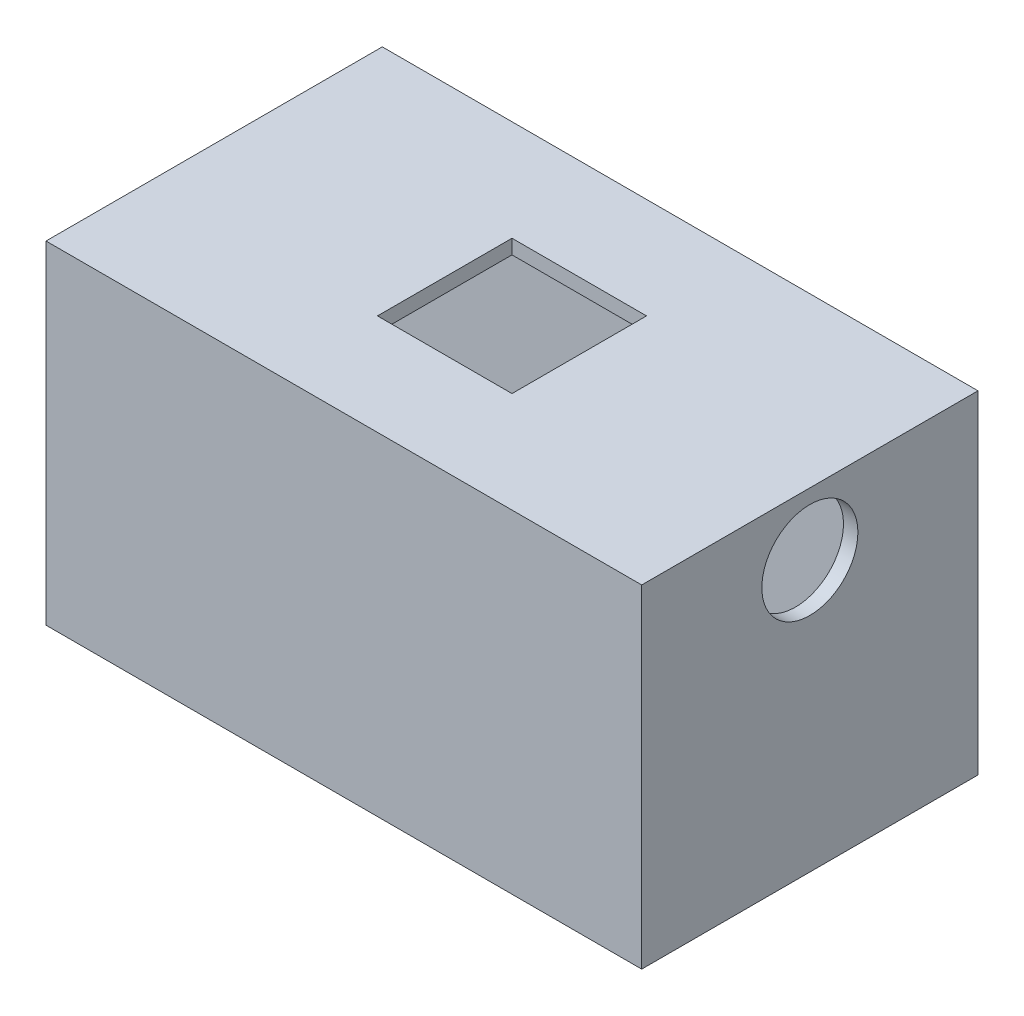
SolidWorks part; units mm, degrees
material "ABS PC"
ref_plane "前视基准面" through (0, 0, 0) normal (0, 0, 1) x (1, 0, 0)
ref_plane "上视基准面" through (0, 0, 0) normal (0, 1, 0) x (1, 0, 0)
ref_plane "右视基准面" through (0, 0, 0) normal (1, 0, 0) x (0, 0, -1)
sketch "草图1" plane through (0, 0, 0) normal (0, 1, 0) x (1, 0, 0)
  line L1 (-28.0032, 22.2518) -> (33.9968, 22.2518)
  line L2 (-28.0032, 22.2518) -> (-28.0032, -12.7482)
  line L3 (-28.0032, -12.7482) -> (33.9968, -12.7482)
  line L4 (33.9968, 22.2518) -> (33.9968, -12.7482)
  point P4 (0, 0)
  dimension "D1" = 35
  dimension "D2" = 62
extrude "凸台-拉伸1" add sketch "草图1" along normal blind 1.5
sketch "草图2" plane through (0, 0, 0) normal (0, -1, 0) x (1, 0, 0)
  line L0 (-28.0032, 12.7482) -> (33.9968, 12.7482) construction
  line L1 (-28.0032, 12.7482) -> (33.9968, 12.7482)
  line L2 (-28.0032, -22.2518) -> (-28.0032, 12.7482) construction
  line L3 (-28.0032, -22.2518) -> (-28.0032, 12.7482)
  line L4 (33.9968, -22.2518) -> (-28.0032, -22.2518) construction
  line L5 (33.9968, -22.2518) -> (-28.0032, -22.2518)
  line L6 (33.9968, 12.7482) -> (33.9968, -22.2518) construction
  line L7 (33.9968, 12.7482) -> (33.9968, -22.2518)
extrude "凸台-拉伸2" add sketch "草图2" along normal up to surface (30.6292 mm away)
sketch "草图3" plane through (0, -30.6292, 0) normal (0, -1, 0) x (1, 0, 0)
  line L0 (32.4968, -20.7518) -> (32.4968, 11.2482) construction
  line L1 (-26.5032, -20.7518) -> (32.4968, -20.7518) construction
  line L2 (-26.5032, 11.2482) -> (-26.5032, -20.7518) construction
  line L3 (32.4968, 11.2482) -> (-26.5032, 11.2482) construction
  line L4 (32.4968, -20.7518) -> (32.4968, 11.2482)
  line L5 (-26.5032, -20.7518) -> (32.4968, -20.7518)
  line L6 (-26.5032, 11.2482) -> (-26.5032, -20.7518)
  line L7 (32.4968, 11.2482) -> (-26.5032, 11.2482)
extrude "切除-拉伸1" cut sketch "草图3" against normal blind 41
sketch "草图4" plane through (0, 1.5, 0) normal (0, 1, 0) x (1, 0, 0)
  line L0 (-28.0032, -12.7482) -> (33.9968, -12.7482) construction
  line L1 (-26.5032, -11.2482) -> (32.4968, -11.2482) construction
  line L2 (32.4968, -11.2482) -> (32.4968, 20.7518) construction
  line L3 (33.9968, -12.7482) -> (33.9968, 22.2518) construction
  line L4 (32.4968, 20.7518) -> (-26.5032, 20.7518) construction
  line L5 (33.9968, 22.2518) -> (-28.0032, 22.2518) construction
  line L6 (-28.0032, 22.2518) -> (-28.0032, -12.7482) construction
  line L7 (-26.5032, 20.7518) -> (-26.5032, -11.2482) construction
  line L8 (-28.0032, -12.7482) -> (33.9968, -12.7482)
  line L9 (-26.5032, -11.2482) -> (32.4968, -11.2482)
  line L10 (32.4968, -11.2482) -> (32.4968, 20.7518)
  line L11 (33.9968, -12.7482) -> (33.9968, 22.2518)
  line L12 (32.4968, 20.7518) -> (-26.5032, 20.7518)
  line L13 (33.9968, 22.2518) -> (-28.0032, 22.2518)
  line L14 (-28.0032, 22.2518) -> (-28.0032, -12.7482)
  line L15 (-26.5032, 20.7518) -> (-26.5032, -11.2482)
extrude "凸台-拉伸3" add sketch "草图4" along normal blind 1
sketch "草图5" plane through (0, 2.5, 0) normal (0, 1, 0) x (1, 0, 0)
  line L0 (33.9968, -12.7482) -> (33.9968, 22.2518) construction
  line L1 (-28.0032, -12.7482) -> (33.9968, -12.7482) construction
  line L2 (-28.0032, 22.2518) -> (-28.0032, -12.7482) construction
  line L3 (33.9968, 22.2518) -> (-28.0032, 22.2518) construction
  line L4 (33.9968, -12.7482) -> (33.9968, 22.2518)
  line L5 (-28.0032, -12.7482) -> (33.9968, -12.7482)
  line L6 (-28.0032, 22.2518) -> (-28.0032, -12.7482)
  line L7 (33.9968, 22.2518) -> (-28.0032, 22.2518)
extrude "凸台-拉伸4" add sketch "草图5" along normal blind 1.5
sketch "草图8" plane through (33.9968, 0, 0) normal (1, 0, 0) x (0, 0, -1)
  line L0 (-12.7482, 4) -> (22.2518, 4) construction
  line L1 (22.2518, 4) -> (22.2518, -30.6292) construction
  line L2 (-12.7482, 4) -> (-12.7482, -30.6292) construction
  circle A0 centre (4.7518, -2.5) radius 5
  dimension "D1" = 10
  dimension "D2" = 6.5
  dimension "D3" = 17.5
  dimension "D4" = 17.5
extrude "切除-拉伸3" cut sketch "草图8" against normal blind 1.5
sketch "草图10" plane through (0, 4, 0) normal (0, 1, 0) x (1, 0, 0)
  line L1 (-4.0032, 11.7518) -> (9.9968, 11.7518)
  line L2 (-4.0032, 11.7518) -> (-4.0032, -2.2482)
  line L3 (-4.0032, -2.2482) -> (9.9968, -2.2482)
  line L4 (9.9968, 11.7518) -> (9.9968, -2.2482)
  line L5 (33.9968, 22.2518) -> (-28.0032, 22.2518) construction
  line L6 (-28.0032, -12.7482) -> (33.9968, -12.7482) construction
  line L7 (-28.0032, 22.2518) -> (-28.0032, -12.7482) construction
  line L8 (33.9968, -12.7482) -> (33.9968, 22.2518) construction
  dimension "D1" = 14
  dimension "D2" = 14
  dimension "D3" = 10.5
  dimension "D4" = 10.5
  dimension "D5" = 24
  dimension "D6" = 24
extrude "切除-拉伸4" cut sketch "草图10" against normal up to next
